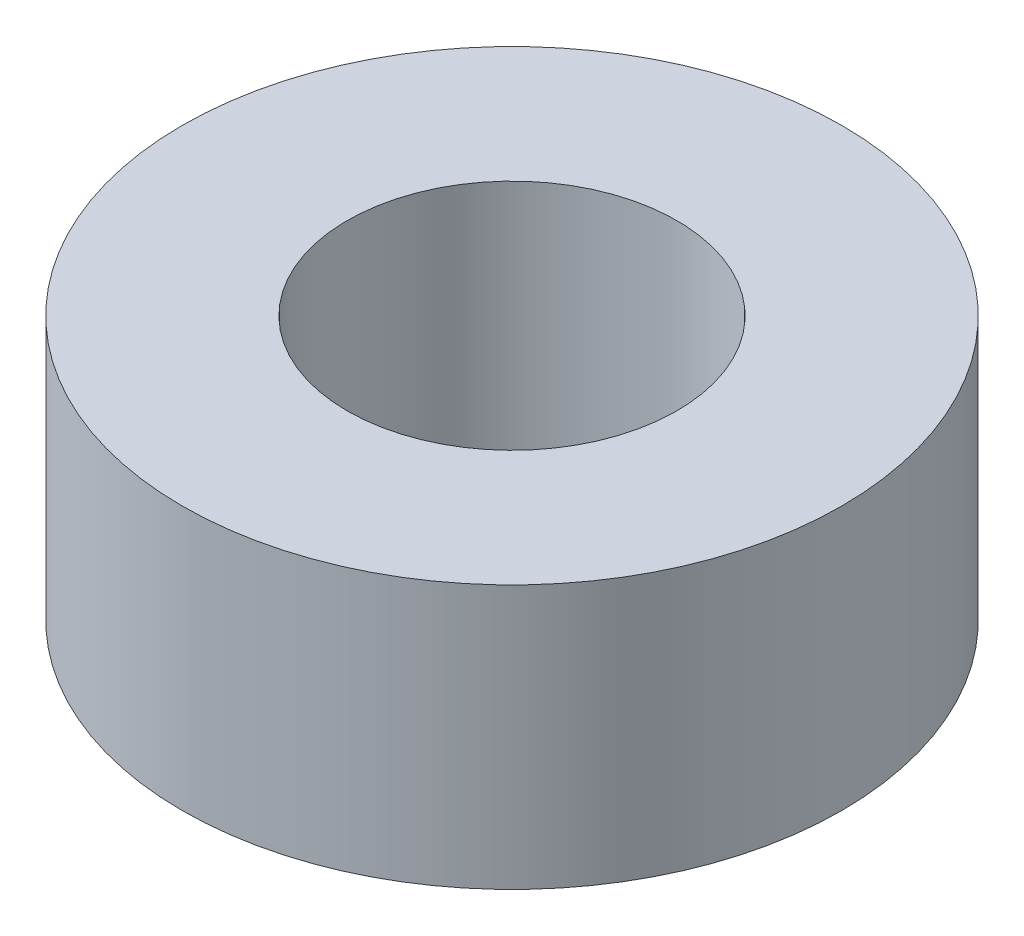
SolidWorks part; units mm, degrees
ref_plane "前视基准面" through (0, 0, 0) normal (0, 0, 1) x (1, 0, 0)
ref_plane "上视基准面" through (0, 0, 0) normal (0, 1, 0) x (1, 0, 0)
ref_plane "右视基准面" through (0, 0, 0) normal (1, 0, 0) x (0, 0, -1)
sketch "草图1" plane through (0, 0, 0) normal (0, 1, 0) x (1, 0, 0)
  circle A0 centre (0, 0) radius 2.5
  circle A1 centre (0, 0) radius 5
  dimension "D1" = 5
  dimension "D2" = 10
extrude "凸台-拉伸1" add sketch "草图1" along normal mid plane 4
